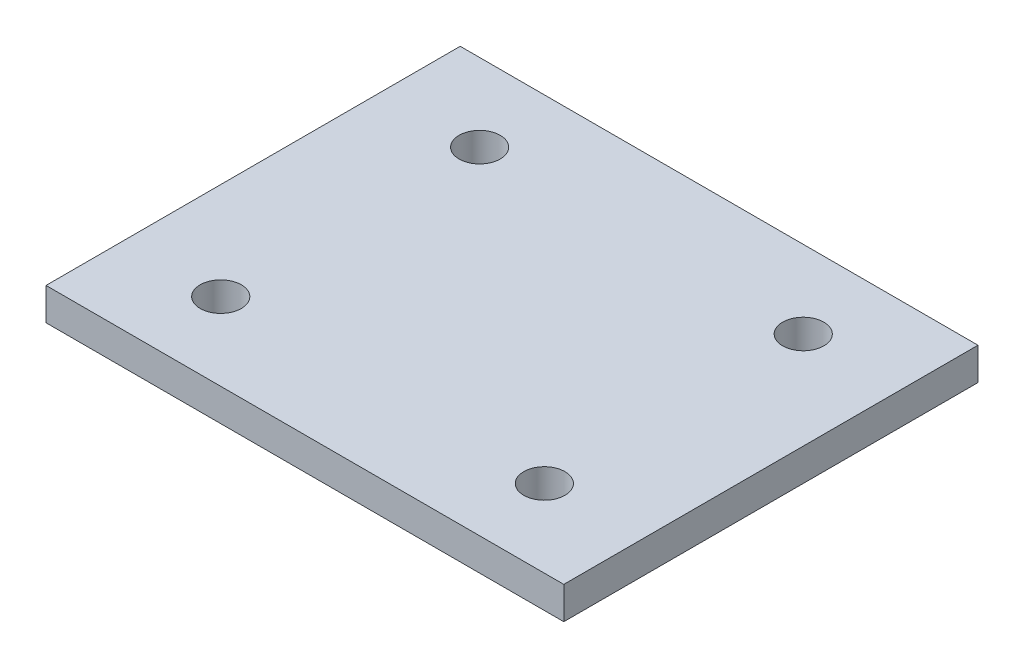
SolidWorks part; units mm, degrees
ref_plane "Front Plane" through (0, 0, 0) normal (0, 0, 1) x (1, 0, 0)
ref_plane "Top Plane" through (0, 0, 0) normal (0, 1, 0) x (1, 0, 0)
ref_plane "Right Plane" through (0, 0, 0) normal (1, 0, 0) x (0, 0, -1)
sketch "Sketch1" plane through (0, 0, 0) normal (0, 1, 0) x (1, 0, 0)
  line L1 (-25.4, -20.32) -> (25.4, -20.32)
  line L2 (-25.4, -20.32) -> (-25.4, 20.32)
  line L3 (-25.4, 20.32) -> (25.4, 20.32)
  line L4 (25.4, -20.32) -> (25.4, 20.32)
  line L5 (-25.4, -20.32) -> (25.4, 20.32) construction
  line L6 (-25.4, 20.32) -> (25.4, -20.32) construction
  circle A0 centre (-15.875, 12.7) radius 2.0193
  circle A1 centre (15.875, 12.7) radius 2.0193
  circle A2 centre (15.875, -12.7) radius 2.0193
  circle A3 centre (-15.875, -12.7) radius 2.0193
  point P0 (0, 0)
  point P14 (0, 0)
  point P15 (0, 0)
  point P16 (0, 0)
  dimension "D1" = 4.0386
  dimension "D2" = 4.0386
  dimension "D3" = 4.0386
  dimension "D4" = 4.0386
  dimension "D5" = 25.4
  dimension "D6" = 50.8
  dimension "D7" = 31.75
extrude "Boss-Extrude1" add sketch "Sketch1" along normal mid plane 3.175 contours L2 L1 L4 L3
equation "\"D2@Sketch1\"=\"D1@Sketch1\""
equation "\"D3@Sketch1\"=\"D1@Sketch1\""
equation "\"D4@Sketch1\"=\"D1@Sketch1\""
